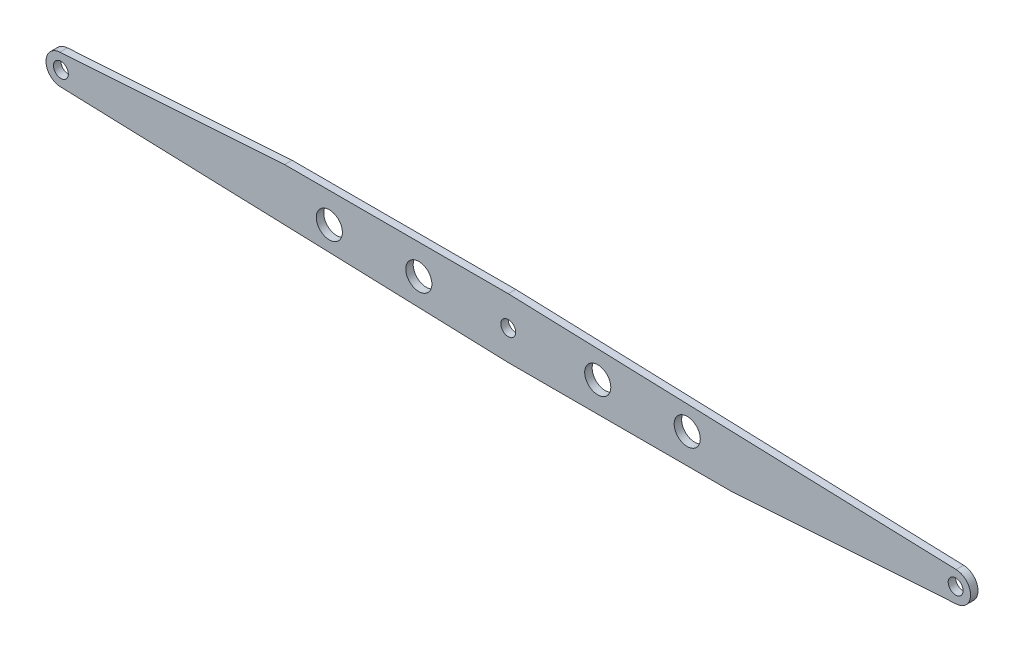
SolidWorks part; units mm, degrees
material "Plain Carbon Steel"
ref_plane "Front Plane" through (0, 0, 0) normal (0, 0, 1) x (1, 0, 0)
ref_plane "Top Plane" through (0, 0, 0) normal (0, 1, 0) x (1, 0, 0)
ref_plane "Right Plane" through (0, 0, 0) normal (1, 0, 0) x (0, 0, -1)
sketch "Sketch1" plane through (0, 0, 0) normal (0, 0, 1) x (1, 0, 0)
  line L4 (0, 40) -> (-300, 40)
  line L5 (0, -40) -> (300, -40)
  line L6 (-300, 40) -> (-601.3275, 19.9559)
  line L7 (0, -40) -> (-600.6659, -19.9889)
  line L8 (0, 40) -> (600.6659, 19.9889)
  line L9 (300, -40) -> (601.3275, -19.9559)
  circle A0 centre (-600, 0) radius 10
  circle A1 centre (600, 0) radius 10
  arc A2 (-601.3275, 19.9559) -> (-600.6659, -19.9889) centre (-600, 0) ccw
  arc A3 (601.3275, -19.9559) -> (600.6659, 19.9889) centre (600, 0) ccw
  circle A4 centre (0, 0) radius 10
  circle A5 centre (-120, 0) radius 17.5
  circle A11 centre (-240, 0) radius 17.5
  circle A13 centre (120, 0) radius 17.5
  circle A14 centre (240, 0) radius 17.5
  circle A15 centre (0, 0) radius 17.5 [skipped]
  dimension "D3" = 20
  dimension "D4" = 20
  dimension "D5" = 40
  dimension "D6" = 40
  dimension "D10" = 20
  dimension "D11" = 35
  dimension "D1" = 600
  dimension "D2" = 600
  dimension "D7" = 40
  dimension "D8" = 300
  dimension "80" = 40
  dimension "D9" = 300
  dimension "D12" = 120
  dimension "D13" = 2
  dimension "D14" = 4
extrude "Boss-Extrude1" add sketch "Sketch1" along normal mid plane 10
